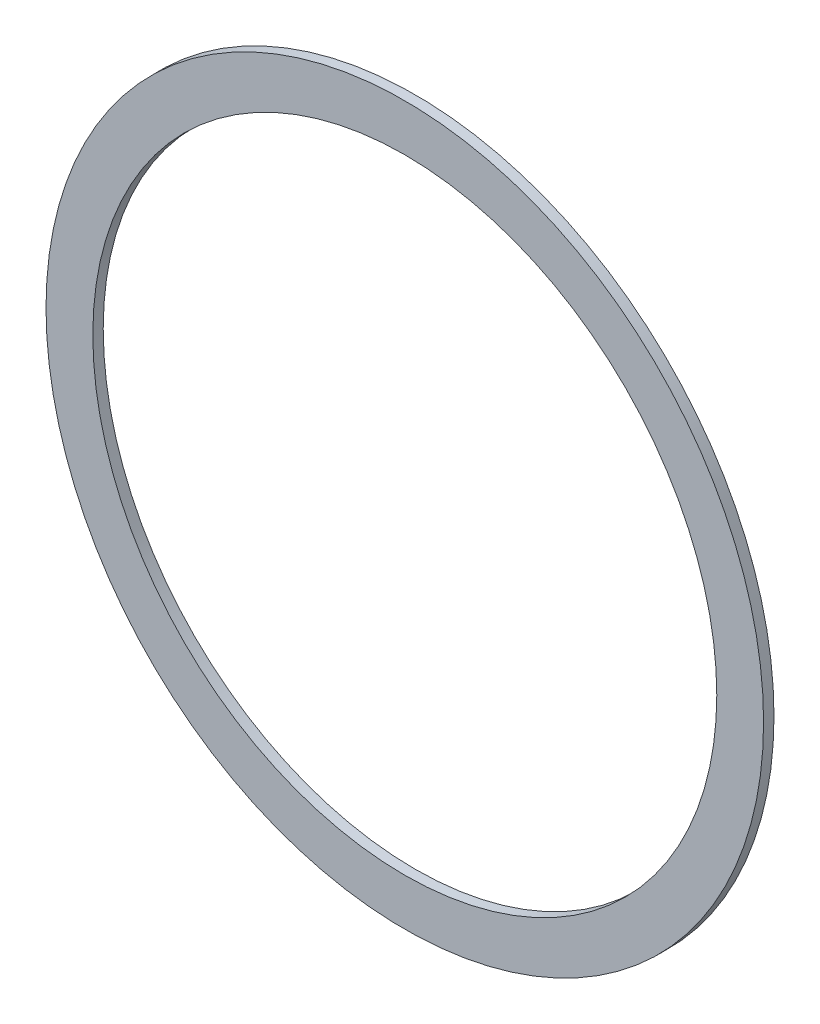
SolidWorks part; units mm, degrees
ref_plane "Front Plane" through (0, 0, 0) normal (0, 0, 1) x (1, 0, 0)
ref_plane "Top Plane" through (0, 0, 0) normal (0, 1, 0) x (1, 0, 0)
ref_plane "Right Plane" through (0, 0, 0) normal (1, 0, 0) x (0, 0, -1)
sketch "Sketch1" plane through (0, 0, 0) normal (0, 0, 1) x (1, 0, 0)
  circle A0 centre (0, 0) radius 60
  circle A1 centre (0, 0) radius 69
  dimension "D1" = 120
  dimension "D2" = 138
extrude "Boss-Extrude1" add sketch "Sketch1" along normal mid plane 2
